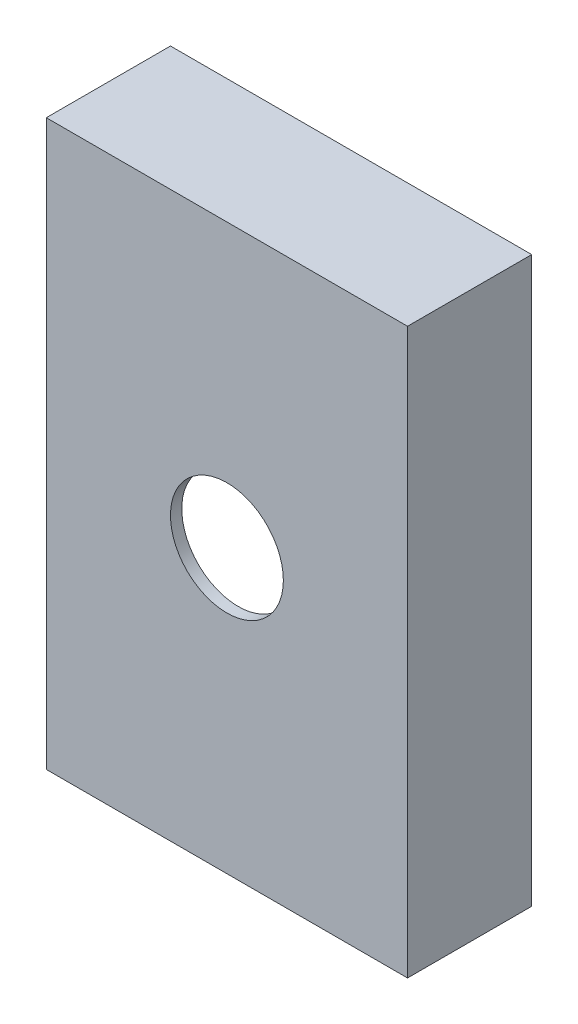
SolidWorks part; units mm, degrees
ref_plane "Plan de face" through (0, 0, 0) normal (0, 0, 1) x (1, 0, 0)
ref_plane "Plan de dessus" through (0, 0, 0) normal (0, 1, 0) x (1, 0, 0)
ref_plane "Plan de droite" through (0, 0, 0) normal (1, 0, 0) x (0, 0, -1)
sketch "Esquisse1" plane through (0, 0, 0) normal (0, 0, 1) x (1, 0, 0)
  line L0 (-5, 5) -> (-155, 5)
  line L1 (0, 0) -> (-160, 0)
  line L2 (0, 0) -> (0, 250)
  line L3 (0, 250) -> (-160, 250)
  line L4 (-160, 0) -> (-160, 250)
  line L5 (-155, 5) -> (-155, 245)
  line L6 (-5, 245) -> (-155, 245)
  line L7 (-5, 5) -> (-5, 245)
  dimension "D1" = 250
  dimension "D2" = 160
  dimension "D3" = 5
extrude "Boss.-Extru.1" add sketch "Esquisse1" along normal blind 50
sketch "Esquisse2" plane through (0, 0, 50) normal (0, 0, 1) x (1, 0, 0)
  line L1 (-160, 250) -> (0, 250)
  line L2 (-160, 250) -> (-160, 0)
  line L3 (-160, 0) -> (0, 0)
  line L4 (0, 250) -> (0, 0)
extrude "Boss.-Extru.2" add sketch "Esquisse2" along normal blind 5
sketch "Esquisse3" plane through (0, 0, 0) normal (0, 0, -1) x (-1, 0, 0)
  line L1 (-50, 250) -> (210, 250)
  line L2 (-50, 250) -> (-50, 0)
  line L3 (-50, 0) -> (210, 0)
  line L4 (210, 250) -> (210, 0)
  line L5 (0, 250) -> (160, 250) construction
  line L6 (160, 250) -> (160, 0) construction
  line L8 (5, 245) -> (155, 245)
  line L9 (5, 245) -> (5, 5)
  line L10 (5, 5) -> (155, 5)
  line L11 (155, 245) -> (155, 5)
  dimension "D1" = 250
  dimension "D2" = 260
  dimension "D3" = 0
  dimension "D4" = 50
sketch "Esquisse4" plane through (0, 0, 55) normal (0, 0, 1) x (1, 0, 0)
  line L0 (50, 250) -> (-210, 250) construction
  line L1 (0, 0) -> (0, 250) construction
  line L2 (-160, 250) -> (0, 0) construction
  circle A0 centre (-80, 125) radius 25
  dimension "D2" = 80
  dimension "D3" = 50
  dimension "D1" = 125
extrude "Enlèv. mat.-Extru.1" cut sketch "Esquisse4" against normal blind 10
